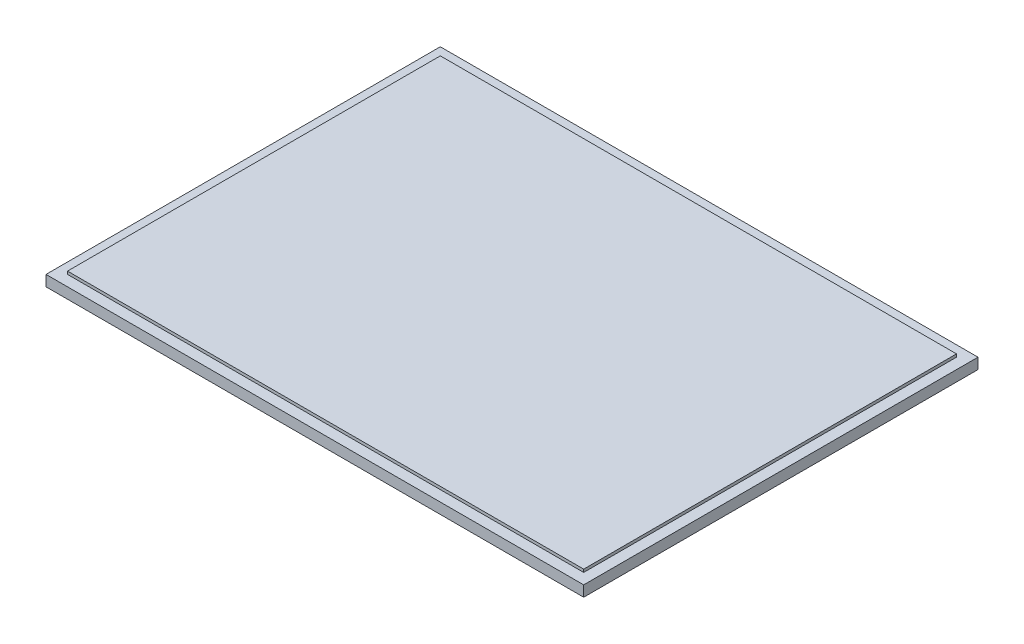
SolidWorks part; units mm, degrees
ref_plane "Front Plane" through (0, 0, 0) normal (0, 0, 1) x (1, 0, 0)
ref_plane "Top Plane" through (0, 0, 0) normal (0, 1, 0) x (1, 0, 0)
ref_plane "Right Plane" through (0, 0, 0) normal (1, 0, 0) x (0, 0, -1)
sketch "Sketch1" plane through (0, 0, 0) normal (0, 1, 0) x (1, 0, 0)
  line L0 (-375, 275) -> (375, 275)
  line L1 (-380, -280) -> (380, -280) construction
  line L2 (-380, -280) -> (-380, 280) construction
  line L3 (-380, 280) -> (380, 280) construction
  line L4 (380, -280) -> (380, 280) construction
  line L5 (-380, -280) -> (380, 280) construction
  line L6 (-380, 280) -> (380, -280) construction
  line L7 (375, -275) -> (375, 275)
  line L8 (-375, -275) -> (375, -275)
  line L9 (-375, -275) -> (-375, 275)
  point P0 (0, 0)
  dimension "D1" = 760
  dimension "D2" = 560
  dimension "D3" = 5
extrude "Boss-Extrude1" add sketch "Sketch1" along normal blind 19
sketch "Sketch2" plane through (0, 19, 0) normal (0, 1, 0) x (1, 0, 0)
  line L0 (375, 275) -> (-375, 275) construction
  line L5 (-370, 0) -> (370, 0) construction
  line L7 (-370, -270) -> (370, -270) construction
  line L8 (-370, -270) -> (-370, 270) construction
  line L9 (-370, 270) -> (370, 270) construction
  line L10 (370, -270) -> (370, 270) construction
  line L11 (-370, -270) -> (370, 270) construction
  line L12 (-370, 270) -> (370, -270) construction
  line L13 (375, -275) -> (375, 275) construction
  line L14 (0, 270) -> (0, -270) construction
  circle A1 centre (-370, 270) radius 1.5
  circle A2 centre (-185, 270) radius 1.5
  circle A3 centre (0, 270) radius 1.5
  circle A4 centre (185, 270) radius 1.5
  circle A5 centre (370, 270) radius 1.5
  circle A6 centre (-370, 90) radius 1.5
  circle A7 centre (-370, -90) radius 1.5
  circle A8 centre (-370, -270) radius 1.5
  circle A9 centre (370, -270) radius 1.5
  circle A10 centre (185, -270) radius 1.5
  circle A11 centre (0, -270) radius 1.5
  circle A12 centre (-185, -270) radius 1.5
  circle A13 centre (-370, -270) radius 1.5
  circle A14 centre (370, -90) radius 1.5
  circle A15 centre (370, 90) radius 1.5
  point P0 (0, 0)
  point P6 (0, 0)
  dimension "D1" = 3
  dimension "D2" = 5
  dimension "D3" = 5
  dimension "D4" = 5
  dimension "D5" = 4
extrude "Cut-Extrude1" [suppressed] cut sketch "Sketch2" against normal through all contours A1 | A2 | A3 | A4 | A5 | A15 | A14 | A9 | A10 | A11 | A12 | A8 | A7 | A6
sketch "Sketch3" plane through (0, 19, 0) normal (0, 1, 0) x (1, 0, 0)
  line L8 (-360, 260) -> (-360, -260)
  line L9 (-360, -260) -> (360, -260)
  line L10 (360, -260) -> (360, 260)
  line L11 (360, 260) -> (-360, 260)
  line L12 (-360, 260) -> (-360, -260)
  line L13 (-360, -260) -> (360, -260)
  line L14 (360, -260) -> (360, 260)
  line L15 (360, 260) -> (-360, 260)
  line L16 (-375, 275) -> (-375, -275)
  line L17 (-375, -275) -> (375, -275)
  line L18 (375, -275) -> (375, 275)
  line L19 (375, 275) -> (-375, 275)
  line L20 (-375, 275) -> (-375, -275)
  line L21 (-375, -275) -> (375, -275)
  line L22 (375, -275) -> (375, 275)
  line L23 (375, 275) -> (-375, 275)
  dimension "D1" = 15
  dimension "D2" = 0
extrude "Cut-Extrude2" cut sketch "Sketch3" against normal blind 4 contours L20 L21 L22 L23
equation "\"Crossbar_Width\"= 80mm"
equation "\"Vertical_Offset\"= \"Crossbar_Width\" / 2"
equation "\"Toolhead_Width\"= 100mm"
equation "\"Mechanical_Buffer\"= 30mm"
equation "\"Z_Interstitial\"= 100mm"
equation "\"Z_Interstitial_Sketch\"= \"Z_Interstitial\" + 1in"
